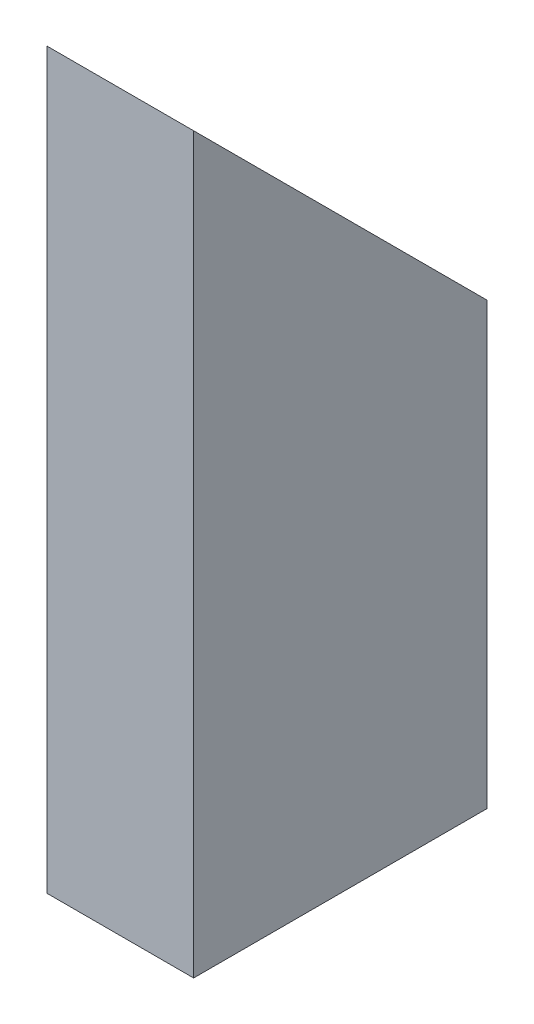
SolidWorks part; units mm, degrees
ref_plane "Front Plane" through (0, 0, 0) normal (0, 0, 1) x (1, 0, 0)
ref_plane "Top Plane" through (0, 0, 0) normal (0, 1, 0) x (1, 0, 0)
ref_plane "Right Plane" through (0, 0, 0) normal (1, 0, 0) x (0, 0, -1)
sketch "Sketch1" plane through (0, 0, 0) normal (0, 1, 0) x (1, 0, 0)
  line L1 (0, 0) -> (25.4, 0)
  line L2 (0, 0) -> (0, 50.8)
  line L3 (0, 50.8) -> (25.4, 50.8)
  line L4 (25.4, 0) -> (25.4, 50.8)
  line L5 (3.175, 3.175) -> (22.225, 3.175)
  line L6 (3.175, 3.175) -> (3.175, 47.625)
  line L7 (3.175, 47.625) -> (22.225, 47.625)
  line L8 (22.225, 3.175) -> (22.225, 47.625)
  dimension "D1" = 50.8
  dimension "D2" = 25.4
  dimension "D3" = 3.175
  dimension "D4" = 3.175
  dimension "D5" = 3.175
  dimension "D6" = 3.175
extrude "Boss-Extrude1" add sketch "Sketch1" along normal blind 127
sketch "Sketch2" plane through (25.4, 0, 0) normal (1, 0, 0) x (0, 0, -1)
  line L0 (0, 127) -> (50.8, 76.2)
  line L1 (50.8, 127) -> (50.8, 0) construction
  line L2 (50.8, 76.2) -> (50.8, 127)
  line L3 (0, 127) -> (50.8, 127) construction
  line L4 (50.8, 127) -> (0, 127)
  dimension "D1" = 76.2
extrude "Cut-Extrude1" cut sketch "Sketch2" against normal blind 127
